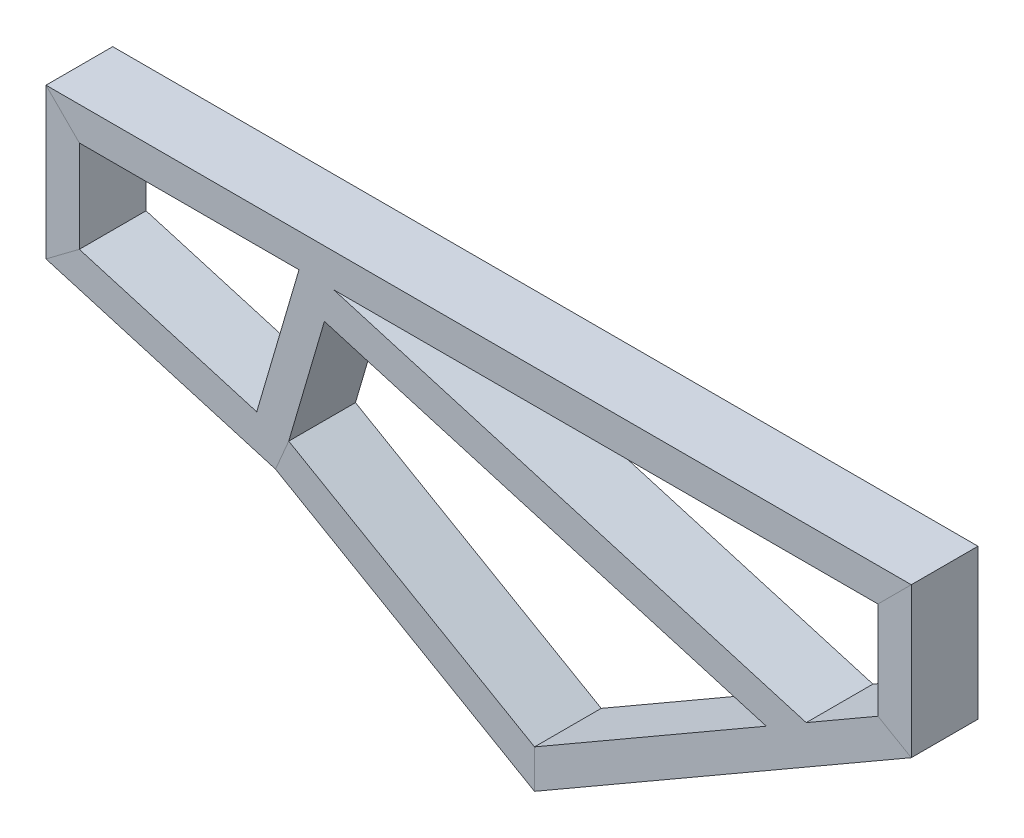
SolidWorks part; units mm, degrees
ref_plane "Спереди" through (0, 0, 0) normal (0, 0, 1) x (1, 0, 0)
ref_plane "Сверху" through (0, 0, 0) normal (0, 1, 0) x (1, 0, 0)
ref_plane "Справа" through (0, 0, 0) normal (1, 0, 0) x (0, 0, -1)
sketch "Эскиз6" plane through (0, 0, 0) normal (1, 0, 0) x (0, 0, -1)
  line L1 (-38.5518, -19.2165) -> (37.4482, -19.2165)
  line L2 (-38.5518, -19.2165) -> (-38.5518, 16.7835)
  line L3 (-38.5518, 16.7835) -> (37.4482, 16.7835)
  line L4 (37.4482, -19.2165) -> (37.4482, 16.7835)
  line L5 (-40.5518, 18.7835) -> (39.4482, 18.7835)
  line L6 (-40.5518, 18.7835) -> (-40.5518, -21.2165)
  line L7 (-40.5518, -21.2165) -> (39.4482, -21.2165)
  line L8 (39.4482, 18.7835) -> (39.4482, -21.2165)
  dimension "D1" = 36
  dimension "D2" = 76
  dimension "D3" = 2
  dimension "D4" = 2
  dimension "D5" = 2
  dimension "D6" = 2
sketch3d "Трехмерный эскиз5"
  line L0 (0, 0, 0) -> (1000, 0, 0)
  line L1 (1000, 0, 0) -> (1000, -150, 0)
  line L2 (1000, -150, 0) -> (566.9873, -400, 0)
  line L3 (566.9873, -400, 0) -> (263.8784, -225, 0)
  line L4 (263.8784, -225, 0) -> (0, -147.5843, 0)
  line L5 (0, -147.5843, 0) -> (0, 0, 0)
  line L6 (263.8784, -225, 0) -> (393.7822, 0, 0)
  line L7 (393.7822, 0, 0) -> (826.7949, -250, 0)
  dimension "D1" = 1000
  dimension "D2" = 150
  dimension "D4" = 400
  dimension "D5" = 225
  dimension "D6" = 350
  dimension "D7" = 275
  dimension "D8" = 500
sweep "По траектории13" add profiles "Эскиз6" path "Трехмерный эскиз5"
sketch "Эскиз14" plane through (-33.8938, -115.53, 0) normal (0.2815, 0.9596, 0) x (0.9596, -0.2815, 0)
  line L0 (319.0859, 39.4482) -> (57.433, 39.4482) construction
  line L1 (319.0859, -40.5518) -> (279.0859, -40.5518)
  line L2 (319.0859, -40.5518) -> (319.0859, 39.4482)
  line L3 (319.0859, 39.4482) -> (279.0859, 39.4482)
  line L4 (279.0859, -40.5518) -> (279.0859, 39.4482)
  point P7 (279.0859, -0.5518)
  dimension "D1" = 40
extrude "Бобышка-Вытянуть1" add sketch "Эскиз14" along normal blind 194
sketch "Эскиз15" plane through (306.1814, -89.8264, 0) normal (0.9596, -0.2815, 0) x (0, 0, -1)
  line L0 (-40.5518, 71.5015) -> (-40.5518, -120.3992) construction
  line L1 (-40.5518, 71.5014) -> (39.4482, 71.5014)
  line L2 (-40.5518, 71.5014) -> (-40.5518, 31.5014)
  line L3 (-40.5518, 31.5014) -> (39.4482, 31.5014)
  line L4 (39.4482, 71.5014) -> (39.4482, 31.5014)
  line L5 (39.4482, 71.5015) -> (39.4482, -120.3992) construction
  line L6 (-40.5518, 71.5015) -> (39.4482, 71.5015) construction
  dimension "D1" = 40
  dimension "D2" = 0.0001
extrude "Бобышка-Вытянуть2" add sketch "Эскиз15" along normal blind 595
